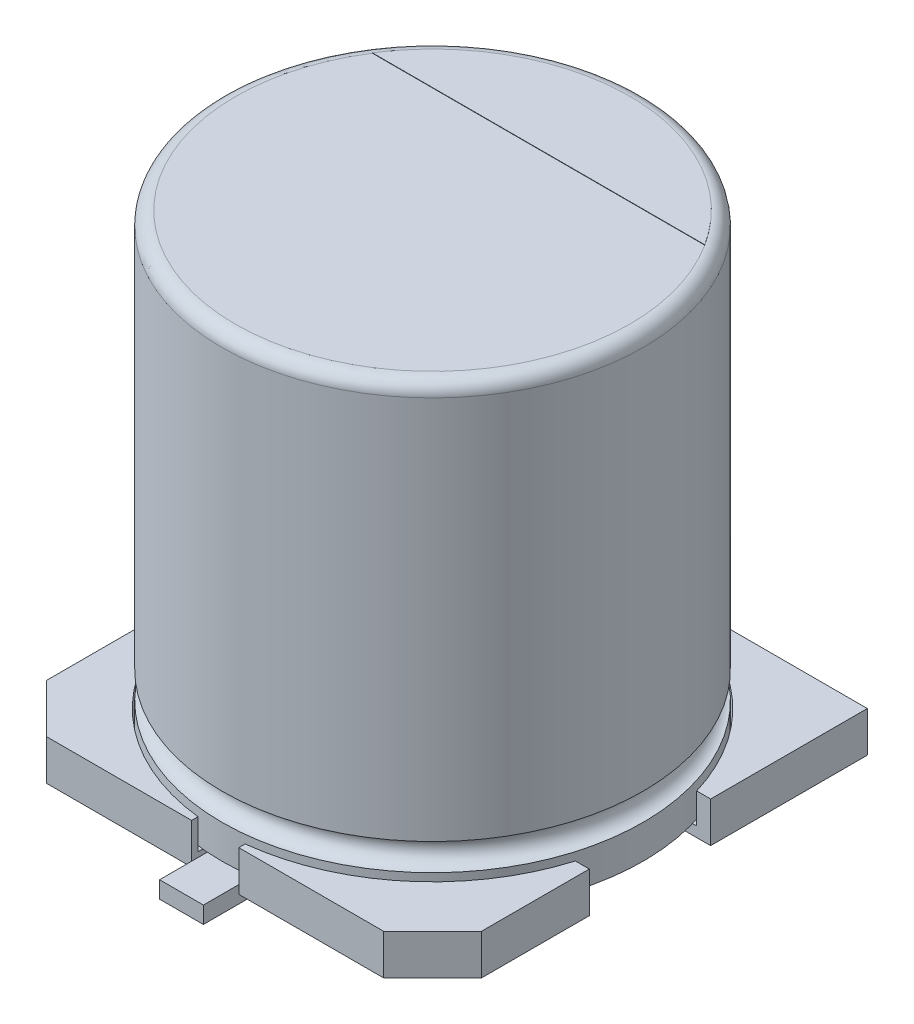
SolidWorks part; units mm, degrees
ref_plane "Front Plane" through (0, 0, 0) normal (0, 0, 1) x (1, 0, 0)
ref_plane "Top Plane" through (0, 0, 0) normal (0, 1, 0) x (1, 0, 0)
ref_plane "Right Plane" through (0, 0, 0) normal (1, 0, 0) x (0, 0, -1)
sketch "Sketch1" plane through (0, 0, 0) normal (0, 1, 0) x (1, 0, 0)
  line L0 (-6.45, 6.45) -> (-0.7, 6.45)
  line L1 (6.45, 6.45) -> (6.45, 1.8)
  line L2 (6.45, -5) -> (5, -6.45)
  line L3 (5, -6.45) -> (0.7, -6.45)
  line L4 (0, -5.9324) -> (0, 5.9324) construction
  line L5 (-6.45, -5) -> (-5, -6.45)
  line L6 (-6.45, 6.45) -> (-6.45, 1.8)
  line L7 (-0.7, -6.45) -> (-0.7, -5.9324)
  line L8 (-0.7, -5.9324) -> (0.7, -5.9324)
  line L9 (-0.7, 6.45) -> (-0.7, 5.9324)
  line L10 (-0.7, 5.9324) -> (0.7, 5.9324)
  line L11 (0.7, 6.45) -> (0.7, 5.9324)
  line L12 (0.7, -6.45) -> (0.7, -5.9324)
  line L13 (-6.45, 1.8) -> (-4.8662, 1.8)
  line L14 (-4.8662, 1.8) -> (-4.8662, -1.8)
  line L15 (-0.7, -6.45) -> (-5, -6.45)
  line L16 (4.8662, 1.8) -> (4.8662, -1.8)
  line L17 (6.45, 1.8) -> (4.8662, 1.8)
  line L18 (6.45, -1.8) -> (4.8662, -1.8)
  line L19 (-6.45, -1.8) -> (-4.8662, -1.8)
  line L20 (-6.45, -1.8) -> (-6.45, -5)
  line L21 (6.45, -1.8) -> (6.45, -5)
  line L22 (4.8662, 0) -> (-4.8662, 0) construction
  line L23 (0.7, 6.45) -> (6.45, 6.45)
  point P0 (0, 0)
  point P17 (0, 5.9324)
  point P19 (0, -5.9324)
  point P25 (0, 0)
  point P31 (4.8662, 0)
  point P32 (-4.8662, 0)
  dimension "D1" = 12.9
  dimension "D2" = 12.9
  dimension "D3" = 135
  dimension "D4" = 10
  dimension "D5" = 1.4
  dimension "D6" = 3.6
extrude "Boss-Extrude1" add sketch "Sketch1" along normal blind 1.2
sketch "Sketch4" plane through (0, 0, 0) normal (0, 1, 0) x (1, 0, 0)
  circle A0 centre (0, 0) radius 6.3
  dimension "D1" = 12.6
extrude "Cut-Extrude1" cut sketch "Sketch4" against normal blind 0.9 from surface at 1.2 starting at face at (0, 1.2, 0.4545)
ref_axis "Axis1" through (0, 22.2235, 0) along (0, -1, 0)
sketch "Sketch3" plane through (0, 0, 0) normal (0, 0, 1) x (1, 0, 0)
  line L0 (-6.25, 13.6) -> (-6.25, 2.2)
  line L1 (-6.25, 1.4) -> (-6.25, 0.4)
  line L2 (-6.25, 0.4) -> (0, 0.4)
  line L3 (0, 22.2235) -> (0, -6.422) construction
  line L4 (-5.85, 14) -> (0, 14)
  line L6 (0, 14) -> (0, 0.4)
  arc A0 (-6.25, 2.2) -> (-6.25, 1.4) centre (-6.25, 1.8) cw
  arc A1 (-5.85, 14) -> (-6.25, 13.6) centre (-5.85, 13.6) ccw
  dimension "D1" = 0.4
  dimension "D2" = 0.4
  dimension "D3" = 14
  dimension "D4" = 6.25
  dimension "D5" = 0.4
  dimension "D6" = 1.4
revolve "Revolve1" add sketch "Sketch3" angle 360 about axis through (0, 22.2235, 0) along (0, -1, 0)
sketch "Sketch5" plane through (0, 0, 0) normal (1, 0, 0) x (0, 0, -1)
  line L0 (-7.45, 0.2) -> (-7.45, -0.3)
  line L1 (-7.45, -0.3) -> (-3.7414, -0.3)
  line L2 (-3.6707, -0.2707) -> (-3.4793, -0.0793)
  line L3 (-3.45, -0.0086) -> (-3.45, 0.2)
  line L4 (-3.45, 0.2) -> (-7.45, 0.2)
  line L5 (0, 22.2235) -> (0, -6.422) construction
  arc A0 (-3.4793, -0.0793) -> (-3.45, -0.0086) centre (-3.55, -0.0086) ccw
  arc A1 (-3.6707, -0.2707) -> (-3.7414, -0.3) centre (-3.7414, -0.2) cw
  point P8 (-3.8131, -0.3)
  point P9 (0, 0)
  point P10 (-7.45, -0.05)
  point P13 (-3.45, -0.05)
  dimension "D6" = 0.1
  dimension "D1" = 7.45
  dimension "D2" = 0.3
  dimension "D3" = 0.5
  dimension "D4" = 225
  dimension "D5" = 4
extrude "Boss-Extrude2" add sketch "Sketch5" along normal blind 0.65 and the other way blind 0.65
mirror "Mirror1" about plane through (0, 0, 0) normal (0, 0, 1) of "Boss-Extrude2"
sketch "Sketch6" plane through (0, 14, 0) normal (0, 1, 0) x (1, 0, 0)
  line L0 (4.9322, 3.1457) -> (-4.9322, 3.1457)
  circle A0 centre (0, 0) radius 5.85 construction
  arc A1 (4.9322, 3.1457) -> (-4.9322, 3.1457) centre (0, 0) ccw
extrude "Boss-Extrude3" add sketch "Sketch6" along normal blind 0.01
